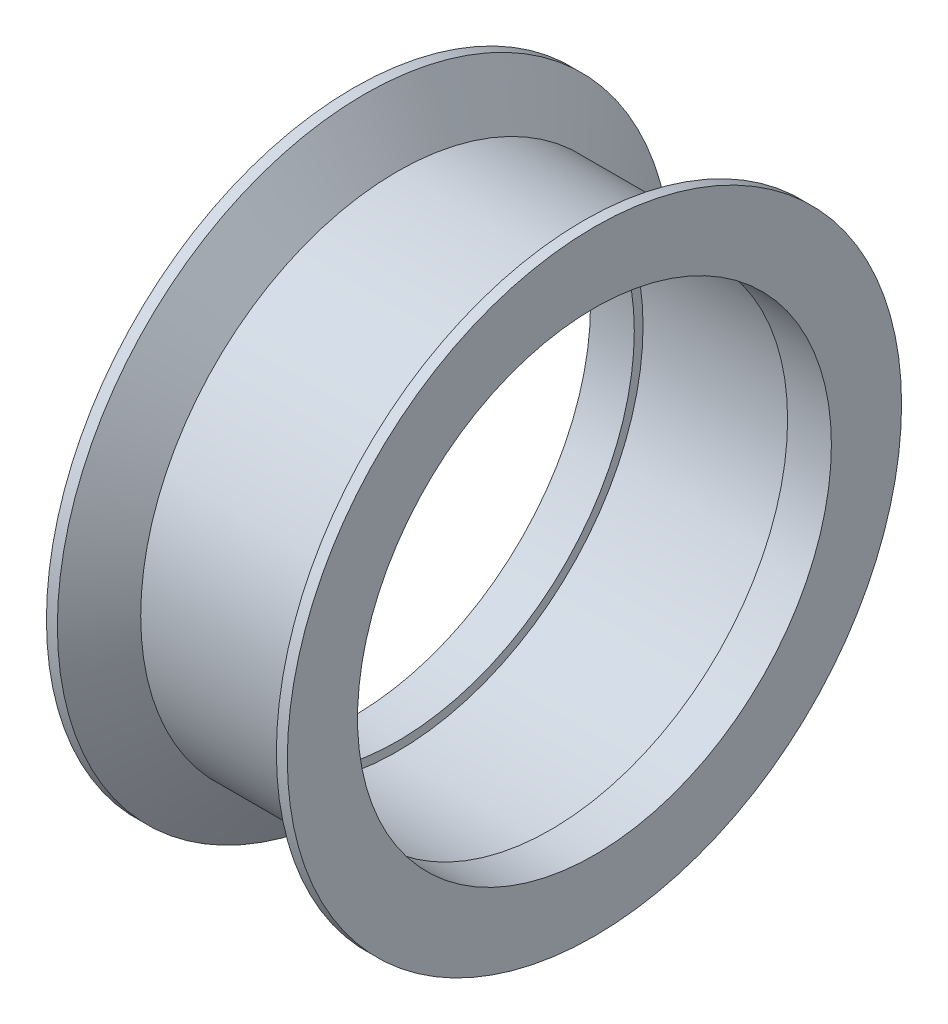
SolidWorks part; units mm, degrees
material "ABS"
ref_plane "Front Plane" through (0, 0, 0) normal (0, 0, 1) x (1, 0, 0)
ref_plane "Top Plane" through (0, 0, 0) normal (0, 1, 0) x (1, 0, 0)
ref_plane "Right Plane" through (0, 0, 0) normal (1, 0, 0) x (0, 0, -1)
sketch "Sketch1" plane through (0, 0, 0) normal (0, 0, 1) x (1, 0, 0)
  line L0 (-3.5, 11.72) -> (-5, 14.0249)
  line L1 (5.5, 10.82) -> (3.5, 10.82)
  line L2 (5.5, 10.82) -> (5.5, 14.0249)
  line L3 (5.5, 14.0249) -> (5, 14.0249)
  line L4 (3.5, 10.82) -> (3.5, 11.22)
  line L5 (3.5, 11.72) -> (-3.5, 11.72)
  line L6 (0, 0) -> (-5.5, 0) construction
  line L7 (3.5, 11.22) -> (-3.5, 11.22)
  line L8 (0, 0) -> (0, 11.22) construction
  line L9 (-3.5, 10.82) -> (-5.5, 10.82)
  line L10 (-3.5, 10.82) -> (-3.5, 11.22)
  line L11 (-5, 14.0249) -> (-5.5, 14.0249)
  line L12 (-5.5, 10.82) -> (-5.5, 14.0249)
  line L13 (3.5, 11.72) -> (5, 14.0249)
  dimension "D1" = 0.5
  dimension "D2" = 0.4
  dimension "D3" = 7
  dimension "D4" = 2
  dimension "D5" = 2.75
  dimension "D6" = 11.22
  dimension "D7" = 0.5
revolve "Revolve1" add sketch "Sketch1" angle 360 about L6
